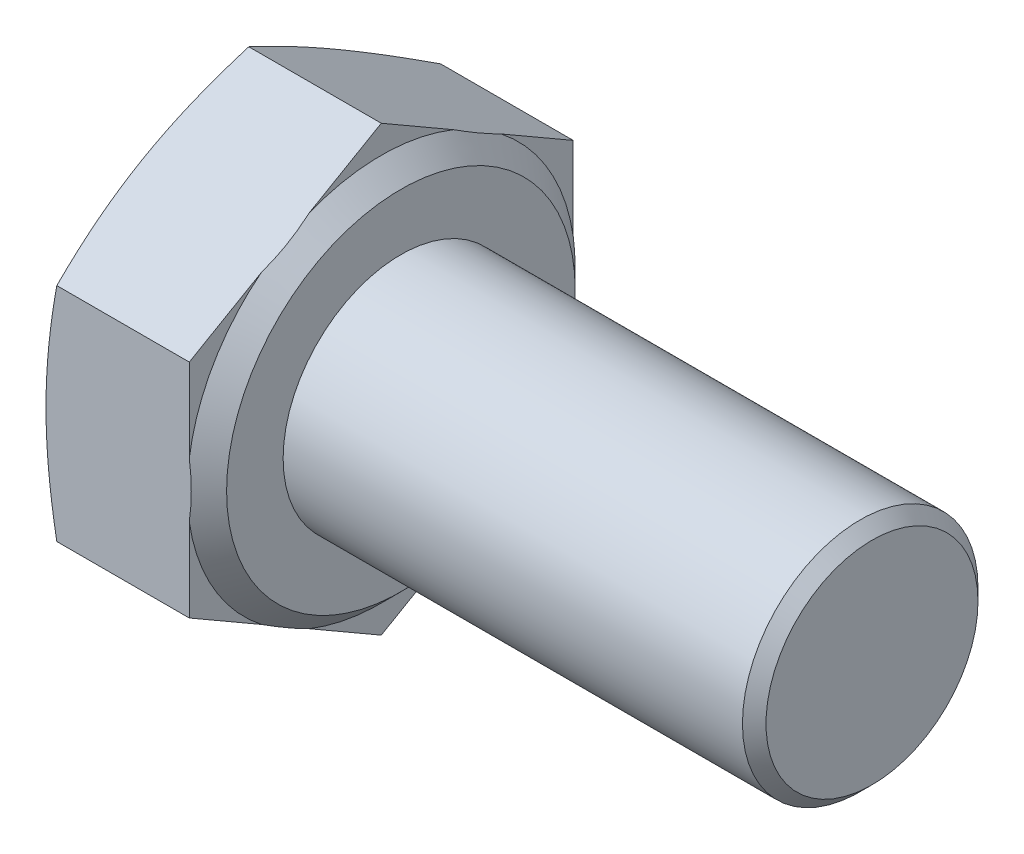
SolidWorks part; units mm, degrees
ref_plane "Front" through (0, 0, 0) normal (0, 0, 1) x (1, 0, 0)
ref_plane "Top" through (0, 0, 0) normal (0, 1, 0) x (1, 0, 0)
ref_plane "Right" through (0, 0, 0) normal (1, 0, 0) x (0, 0, -1)
sketch "Sketch2" plane through (0, 0, 0) normal (1, 0, 0) x (0, 0, -1)
  line L1 (4.89, -2.8232) -> (4.89, 2.8232)
  line L2 (4.89, 2.8232) -> (0, 5.6465)
  line L3 (0, 5.6465) -> (-4.89, 2.8232)
  line L4 (-4.89, 2.8232) -> (-4.89, -2.8232)
  line L5 (-4.89, -2.8232) -> (0, -5.6465)
  line L6 (0, -5.6465) -> (4.89, -2.8232)
  circle A0 centre (0, 0) radius 4.89 construction
  dimension "s" = 9.78
extrude "BaseHead" add sketch "Sketch2" along normal blind 4.15
sketch "Sketch3" plane through (0, 0, 0) normal (0, 0, 1) x (1, 0, 0)
  line L0 (4.15, 5.6465) -> (4.15, 4.44)
  line L2 (4.15, 4.44) -> (3.65, 4.94)
  line L3 (3.65, 4.94) -> (3.65, 5.6465)
  line L5 (3.65, 5.6465) -> (4.15, 5.6465)
  line L6 (-0.9571, 0) -> (7.6478, 0) construction
  line L7 (4.15, 5.6465) -> (0, 5.6465) construction
  dimension "D1" = 45
  dimension "c" = 0.5
  dimension "Dw" = 8.88
revolve "BearingFace" cut sketch "Sketch3" angle 360 about L6
sketch "Sketch4" plane through (0, 0, 0) normal (0, 0, 1) x (1, 0, 0)
  line L0 (-0.4935, 0) -> (3.5626, 0) construction
  line L2 (0, 5.6465) -> (0.2753, 5.6465)
  line L4 (0.2753, 5.6465) -> (0, 4.89)
  line L6 (0, 4.89) -> (0, 5.6465)
  line L7 (3.65, 5.6465) -> (0, 5.6465) construction
  dimension "D1" = 20
  dimension "D2" = 9.78
revolve "HeadChamfer" cut sketch "Sketch4" angle 360 about L0
sketch "Sketch5" plane through (4.15, 0, 0) normal (1, 0, 0) x (0, 0, -1)
  circle A0 centre (0, 0) radius 3
  dimension "d" = 6
extrude "BaseBody" add sketch "Sketch5" along normal blind 12
cosmetic thread "ThreadCosmetic1" parameters "D2"=4.917
chamfer "Chamfer1" distance 0.3 angle 45 1 edges at (16.15, 0, -3)
fillet "HeadFillet" [suppressed] radius 0.25
sketch "Sketch6" plane through (0, 0, 0) normal (0, 0, 1) x (1, 0, 0)
  line L0 (4.15, 3.5415) -> (4.6915, 3.5415)
  line L1 (4.6915, 3.5415) -> (4.6915, 3)
  line L2 (4.6915, 3) -> (4.4207, 2.531)
  line L3 (4.4207, 2.531) -> (4.15, 3)
  line L4 (4.15, 3) -> (4.15, 3.5415)
  line L5 (15.85, 3) -> (4.15, 3) construction
  line L6 (4.15, -4.44) -> (4.15, 4.44) construction
  dimension "D1" = 0.5415
revolve "Cut-Revolve10" [suppressed] cut sketch "Sketch6" angle 360 about axis through (-0.9571, 0, 0) along (1, 0, 0)
pattern_linear "LPattern10" [suppressed] count 18
equation "\"D2@Sketch4\" = \"s@Sketch2\""
equation "\"D1@Chamfer1\" = 0.05 * \"d@Sketch5\""
equation "\"D1@Sketch6\" =  ( \"d@Sketch5\" - \"D2@ThreadCosmetic1\" )  / 2"
equation "\"pitch@LPattern10\" = \"D1@Sketch6\" * 1.2"
equation "\"D1@LPattern10\" = \"l@BaseBody\" / \"pitch@LPattern10\""
